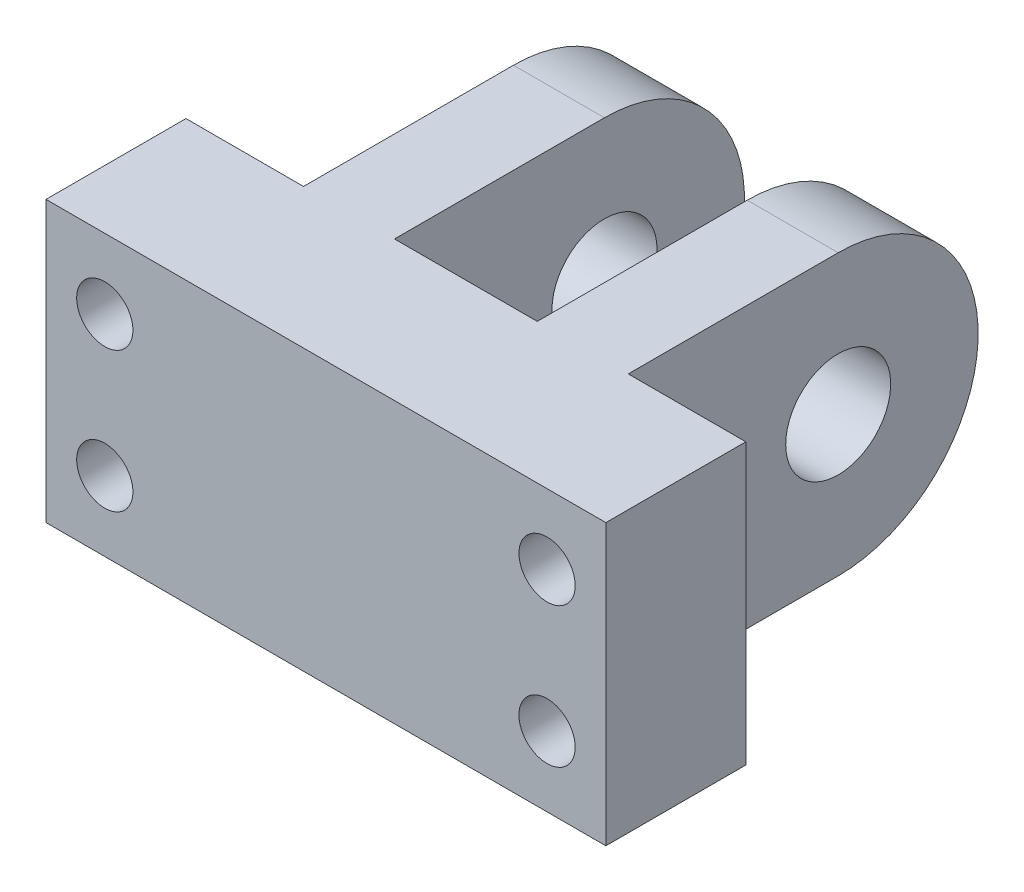
SolidWorks part; units mm, degrees
ref_plane "Front Plane" through (0, 0, 0) normal (0, 0, 1) x (1, 0, 0)
ref_plane "Top Plane" through (0, 0, 0) normal (0, 1, 0) x (1, 0, 0)
ref_plane "Right Plane" through (0, 0, 0) normal (1, 0, 0) x (0, 0, -1)
sketch "Sketch1" plane through (0, 0, 0) normal (1, 0, 0) x (0, 0, -1)
  line L1 (0, 0) -> (31.75, 0)
  line L2 (0, 0) -> (0, 25.4)
  line L3 (0, 25.4) -> (31.75, 25.4)
  circle A0 centre (31.75, 12.7) radius 4.7625
  arc A1 (31.75, 25.4) -> (31.75, 0) centre (31.75, 12.7) cw
  point P1 (0, 0)
  point P7 (71.0237, 56.8731)
  point P10 (37.3145, 10.5454)
  point P11 (0, 0)
  dimension "D1" = 9.525
  dimension "D3" = 12.7
  dimension "D2" = 31.75
extrude "Boss-Extrude1" add sketch "Sketch1" along normal blind 50.8
sketch "Sketch2" plane through (0, 0, 0) normal (0, -1, 0) x (1, 0, 0)
  line L0 (50.8, -12.7) -> (40.132, -12.7)
  line L1 (50.8, 0) -> (50.8, -31.75) construction
  line L2 (40.132, -12.7) -> (40.132, -44.45)
  line L3 (40.132, -44.45) -> (31.877, -44.45)
  line L4 (31.877, -44.45) -> (31.877, -12.7)
  line L5 (31.877, -12.7) -> (18.923, -12.7)
  line L6 (18.923, -12.7) -> (18.923, -44.45)
  line L7 (18.923, -44.45) -> (10.668, -44.45)
  line L8 (10.668, -44.45) -> (10.668, -12.7)
  line L9 (10.668, -12.7) -> (0, -12.7)
  line L10 (0, 0) -> (0, -31.75) construction
  line L11 (40.132, -12.7) -> (31.877, -12.7) construction
  line L12 (18.923, -12.7) -> (10.668, -12.7) construction
  line L13 (50.8, -12.7) -> (50.8, -50.8)
  line L14 (50.8, -50.8) -> (0, -50.8)
  line L15 (0, -50.8) -> (0, -12.7)
  point P4 (0, 0)
  point P18 (0, 0)
  dimension "D1" = 12.954
  dimension "D2" = 8.255
  dimension "D3" = 12.7
  dimension "D4" = 6.35
extrude "Cut-Extrude1" cut sketch "Sketch2" against normal through all
sketch "Sketch3" plane through (0, 0, -12.7) normal (0, 0, -1) x (-1, 0, 0)
  line L0 (-5.334, 25.4) -> (-5.334, 0) construction
  line L1 (-10.668, 25.4) -> (0, 25.4) construction
  line L2 (-10.668, 0) -> (0, 0) construction
  line L3 (-45.466, 0) -> (-45.466, 25.4) construction
  line L4 (-50.8, 0) -> (-40.132, 0) construction
  line L5 (-50.8, 25.4) -> (-40.132, 25.4) construction
  line L6 (-45.466, 19.05) -> (-5.334, 19.05) construction
  line L7 (-5.334, 6.35) -> (-45.466, 6.35) construction
  line L8 (-5.334, 6.35) -> (0, 0) construction
  line L9 (-45.466, 19.05) -> (-50.8, 25.4) construction
  dimension "D1" = 12.7
hole_wizard "CBORE for #10 Socket Head Cap Screw1" positions "Sketch4" profile "Sketch5" counterbore size "#10" standard "ANSI Inch" end condition through all
sketch "Sketch4" plane through (0, 0, -12.7) normal (0, 0, -1) x (-1, 0, 0)
  point P0 (-45.466, 6.35)
  point P3 (-45.466, 19.05)
  point P6 (-5.334, 19.05)
  point P9 (-5.334, 6.35)
sketch "Sketch5" plane through (45.466, 6.35, -12.7) normal (1, 0, 0) x (0, 1, 0)
  line L0 (0, 0) -> (0, 12.7)
  line L1 (0, 12.7) -> (2.5527, 12.7)
  line L3 (2.5527, 12.7) -> (2.5527, 4.826)
  line L4 (2.5527, 4.826) -> (4.7625, 4.826)
  line L5 (4.7625, 4.826) -> (4.7625, 0)
  line L7 (4.7625, 0) -> (0, 0)
  line L11 (0, -6.35) -> (0, 107.95) construction
  dimension "Thru Hole Dia." = 5.1054
  dimension "Thru Hole Depth" = 12.7
  dimension "C'Bore Dia." = 9.525
  dimension "C'Bore Depth" = 4.826
